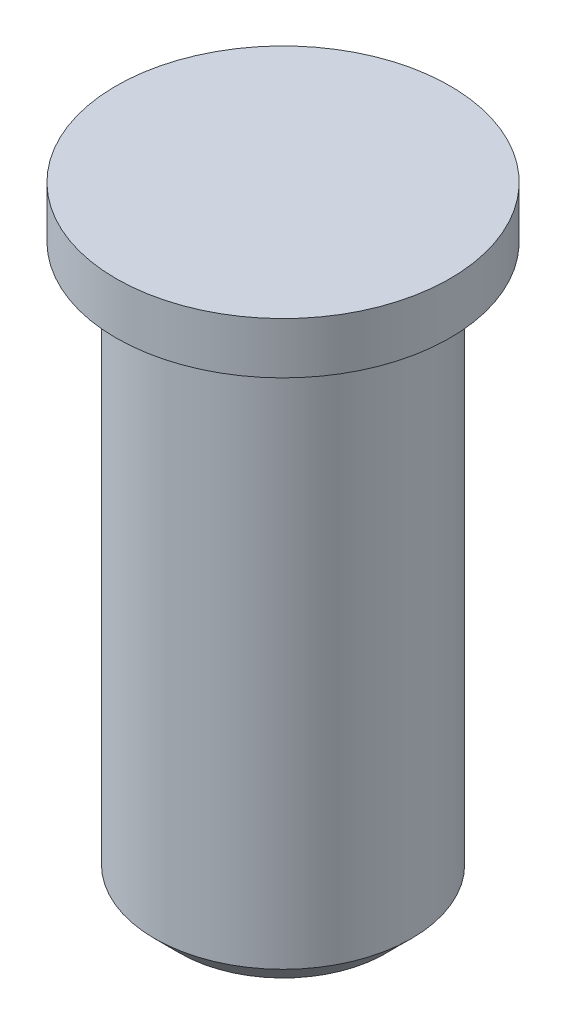
SolidWorks part; units mm, degrees
material "acero"
ref_plane "Alzado" through (0, 0, 0) normal (0, 0, 1) x (1, 0, 0)
ref_plane "Planta" through (0, 0, 0) normal (0, 1, 0) x (1, 0, 0)
ref_plane "Vista lateral" through (0, 0, 0) normal (1, 0, 0) x (0, 0, -1)
sketch "Croquis1" plane through (0, 0, 0) normal (0, 0, 1) x (1, 0, 0)
  line L0 (0, 0) -> (0, -60.9498) construction
  line L1 (0, 0) -> (3.25, 0)
  line L2 (3.25, 0) -> (3.25, -1)
  line L3 (3.25, -1) -> (2.5, -1)
  line L4 (2.5, -1) -> (2.5, -12)
  line L5 (2.5, -12) -> (0, -12)
  line L6 (0, -12) -> (0, 0)
  dimension "D1" = 12
  dimension "D2" = 1
  dimension "D3" = 6.5
  dimension "D4" = 5
revolve "Revolución1" add sketch "Croquis1" angle 360 about L0
chamfer "Chaflán1" distance 0.5 angle 45 1 edges at (0, -12, 2.5)
